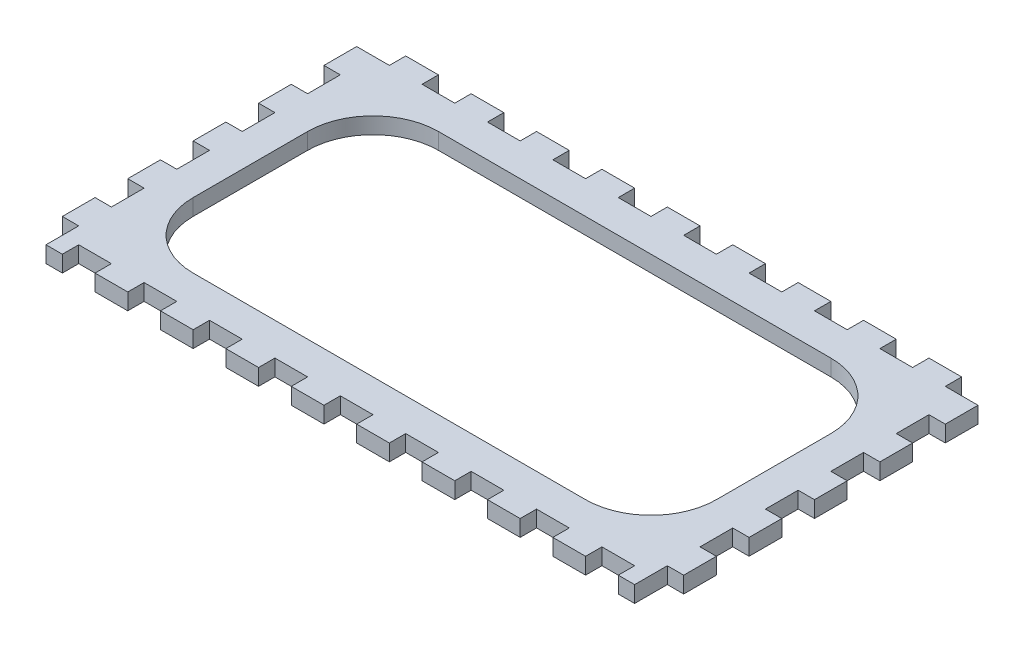
SolidWorks part; units mm, degrees
material "Pine"
ref_plane "Front Plane" through (0, 0, 0) normal (0, 0, 1) x (1, 0, 0)
ref_plane "Top Plane" through (0, 0, 0) normal (0, 1, 0) x (1, 0, 0)
ref_plane "Right Plane" through (0, 0, 0) normal (1, 0, 0) x (0, 0, -1)
sketch "Sketch2" plane through (0, 0, 0) normal (0, 1, 0) x (1, 0, 0)
  line L1 (0, 0) -> (241.3, 0)
  line L2 (0, 0) -> (0, 133.35)
  line L3 (0, 133.35) -> (241.3, 133.35)
  line L4 (241.3, 0) -> (241.3, 133.35)
  dimension "D1" = 133.35
  dimension "D2" = 241.3
extrude "Boss-Extrude1" add sketch "Sketch2" along normal blind 6.35
sketch "Sketch3" plane through (0, 6.35, 0) normal (0, 1, 0) x (1, 0, 0)
  line L1 (0, 0) -> (6.35, 0)
  line L2 (0, 0) -> (0, 12.7)
  line L3 (0, 12.7) -> (6.35, 12.7)
  line L4 (6.35, 0) -> (6.35, 12.7)
  line L5 (241.3, 0) -> (234.95, 0)
  line L6 (241.3, 0) -> (241.3, 12.7)
  line L7 (241.3, 12.7) -> (234.95, 12.7)
  line L8 (234.95, 0) -> (234.95, 12.7)
  dimension "D1" = 12.7
  dimension "D2" = 6.35
extrude "Cut-Extrude1" cut sketch "Sketch3" against normal through all
pattern_linear "LPattern1" count 6 spacing 25.4 along (0, 0, -1) of "Cut-Extrude1"
sketch "Sketch4" plane through (0, 6.35, 0) normal (0, 1, 0) x (1, 0, 0)
  line L0 (6.35, 0) -> (234.95, 0) construction
  line L1 (215.9, 0) -> (228.6, 0)
  line L2 (215.9, 0) -> (215.9, 6.35)
  line L3 (215.9, 6.35) -> (228.6, 6.35)
  line L4 (228.6, 0) -> (228.6, 6.35)
  line L6 (234.95, 12.7) -> (234.95, 0) construction
  line L7 (241.3, 12.7) -> (234.95, 12.7) construction
  dimension "D1" = 6.35
extrude "Cut-Extrude2" cut sketch "Sketch4" against normal through all
pattern_linear "LPattern2" count 10 spacing 25.4 along (-1, 0, 0) of "Cut-Extrude2"
sketch "Sketch5" plane through (0, 6.35, 0) normal (0, 1, 0) x (1, 0, 0)
  line L0 (234.95, 133.35) -> (6.35, 133.35) construction
  line L1 (12.7, 133.35) -> (0, 133.35)
  line L2 (12.7, 133.35) -> (12.7, 127)
  line L3 (12.7, 127) -> (0, 127)
  line L4 (0, 133.35) -> (0, 127)
  line L5 (0, 127) -> (0, 114.3) construction
extrude "Cut-Extrude3" cut sketch "Sketch5" against normal through all
pattern_linear "LPattern3" count 10 spacing 25.4 along (1, 0, 0) of "Cut-Extrude3"
sketch "Sketch6" plane through (0, 6.35, 0) normal (0, 1, 0) x (1, 0, 0)
  line L0 (25.4, 127) -> (38.1, 127) construction
  line L1 (19.05, 114.3) -> (222.25, 114.3)
  line L2 (19.05, 114.3) -> (19.05, 19.05)
  line L3 (19.05, 19.05) -> (222.25, 19.05)
  line L4 (222.25, 114.3) -> (222.25, 19.05)
  line L5 (6.35, 101.6) -> (6.35, 114.3) construction
  line L6 (50.8, 6.35) -> (38.1, 6.35) construction
  line L7 (234.95, 63.5) -> (234.95, 50.8) construction
  dimension "D1" = 12.7
  dimension "D2" = 12.7
  dimension "D3" = 12.7
  dimension "D4" = 12.7
extrude "Cut-Extrude4" cut sketch "Sketch6" against normal through all
fillet "Fillet1" radius 25.4 4 edges at (222.25, 3.175, -19.05) (222.25, 3.175, -114.3) (19.05, 3.175, -19.05) (19.05, 3.175, -114.3)
